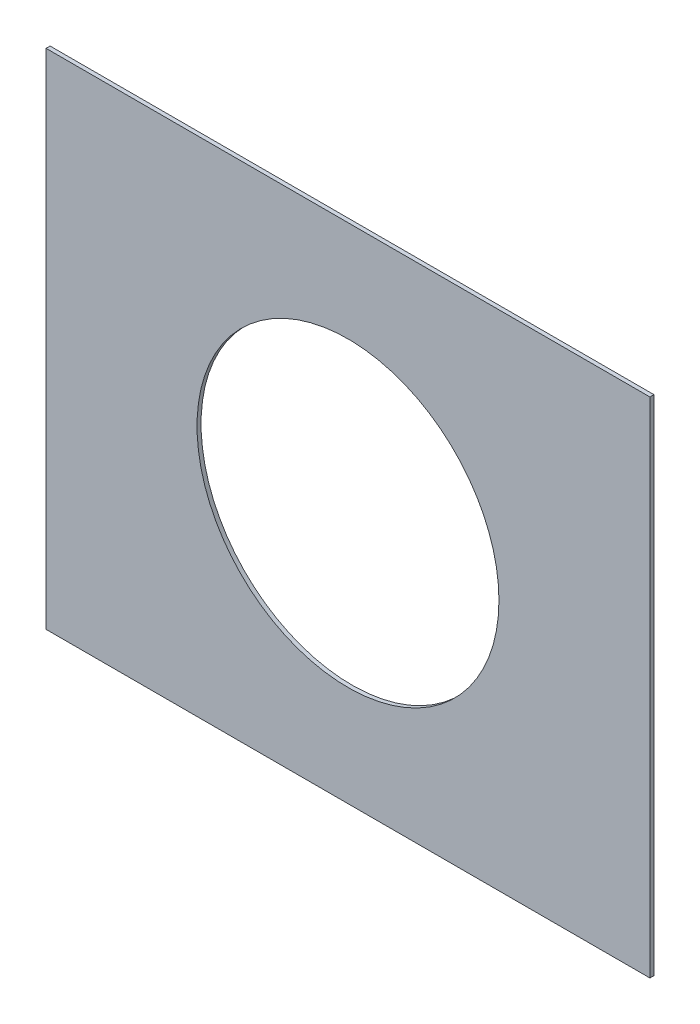
SolidWorks part; units mm, degrees
ref_plane "Front Plane" through (0, 0, 0) normal (0, 0, 1) x (1, 0, 0)
ref_plane "Top Plane" through (0, 0, 0) normal (0, 1, 0) x (1, 0, 0)
ref_plane "Right Plane" through (0, 0, 0) normal (1, 0, 0) x (0, 0, -1)
sketch "Sketch1" plane through (0, 0, 0) normal (0, 0, 1) x (1, 0, 0)
  line L0 (-150, 0) -> (0, 0) construction
  line L1 (-150, 125) -> (150, 125)
  line L2 (-150, 125) -> (-150, -125)
  line L3 (-150, -125) -> (150, -125)
  line L4 (150, 125) -> (150, -125)
  line L5 (0, 0) -> (0, -125) construction
  circle A0 centre (0, 0) radius 75
  dimension "D1" = 150
  dimension "D2" = 300
  dimension "D3" = 250
extrude "Boss-Extrude1" add sketch "Sketch1" along normal blind 2
sketch "Sketch4" plane through (0, 0, 2) normal (0, 0, 1) x (1, 0, 0)
  line L0 (-150, 125) -> (-150, -125) construction
  line L1 (142.5, 117.5) -> (-142.5, 117.5)
  line L2 (142.5, 117.5) -> (142.5, -117.5)
  line L3 (142.5, -117.5) -> (-142.5, -117.5)
  line L4 (-142.5, 117.5) -> (-142.5, -117.5)
  line L5 (142.5, 117.5) -> (-142.5, -117.5) construction
  line L6 (142.5, -117.5) -> (-142.5, 117.5) construction
  line L7 (150, 125) -> (-150, 125) construction
  line L8 (-142.5, -98) -> (142.5, -98) construction
  line L9 (-150, -125) -> (150, -125) construction
  line L11 (-142.5, 0) -> (142.5, 0) construction
  point P0 (0, 0)
  point P10 (0, 0)
  point P11 (142.5, 98)
  point P12 (-142.5, 0)
  point P13 (-142.5, -98)
  point P15 (142.5, 0)
  point P16 (-142.5, 98)
  point P17 (142.5, -98)
  point P22 (0, 0)
  dimension "D1" = 7.5
  dimension "D2" = 7.5
  dimension "D3" = 27
